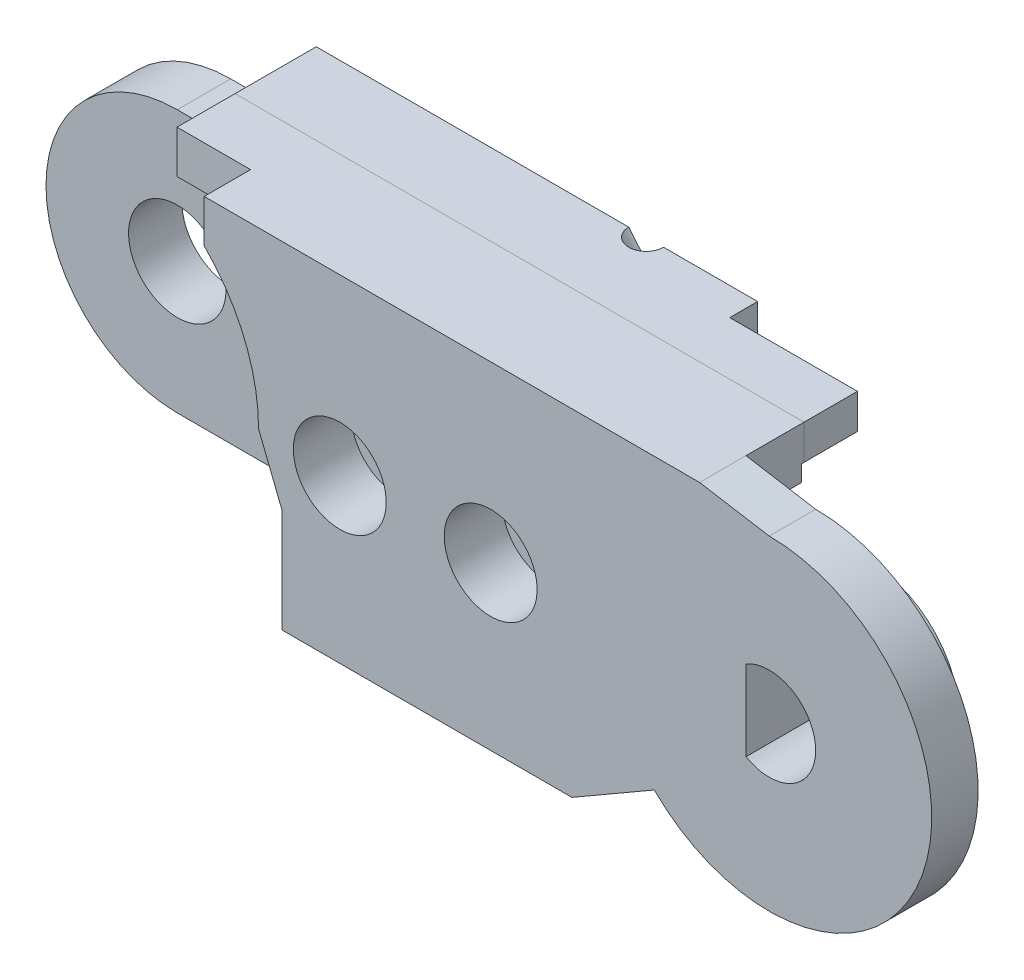
SolidWorks part; units mm, degrees
ref_plane "Front Plane" through (0, 0, 0) normal (0, 0, 1) x (1, 0, 0)
ref_plane "Top Plane" through (0, 0, 0) normal (0, 1, 0) x (1, 0, 0)
ref_plane "Right Plane" through (0, 0, 0) normal (1, 0, 0) x (0, 0, -1)
sketch "Sketch3" plane through (0, 0, 0) normal (0, 0, 1) x (1, 0, 0)
  line L7 (8, 0) -> (9, -2.5)
  line L11 (30, 7) -> (27, 7.5)
  line L13 (0, 7) -> (0, 7.5) construction
  line L14 (0, 7.5) -> (-22.3287, 7.5) construction
  line L15 (0, 5.3) -> (-14, 5.3) construction
  line L16 (0, 4) -> (-14, 4) construction
  line L17 (-14, 4) -> (-14, 5.3) construction
  line L18 (5.6569, 5.6569) -> (5.6569, 7.5)
  line L19 (5.6569, 7.5) -> (27, 7.5)
  line L20 (21.5, -7) -> (9, -7)
  line L21 (9, -7) -> (9, -2.5)
  line L23 (25.0503, -4.9497) -> (21.5, -7)
  arc A4 (8, 0) -> (5.6569, 5.6569) centre (0, 0) ccw
  arc A5 (25.0503, -4.9497) -> (30, 7) centre (30, 0) ccw
  circle A6 centre (0, 0) radius 7 construction
  circle A7 centre (0, 0) radius 3.9 construction
  circle A8 centre (0, 0) radius 5.3 construction
  circle A9 centre (0, 0) radius 4 construction
  dimension "D10" = 0.5
  dimension "D17" = 14
  dimension "D5" = 135
  dimension "D6" = 12.5
  dimension "D7" = 4.5
  dimension "D8" = 1
  dimension "D9" = 45
  dimension "D11" = 1.8431
  dimension "D12" = 30
  dimension "D14" = 3
extrude "Boss-Extrude1" add sketch "Sketch3" along normal blind 2 contours A5 L11 L19 L18 A4 L7 L21 L20 L23
sketch "Sketch20" plane through (0, 0, 0) normal (0, 0, 1) x (1, 0, 0)
  line L0 (0, 7) -> (0, 7.5) construction
  line L1 (0, 7.5) -> (-19.4737, 7.5) construction
  line L2 (0, 5.3) -> (-14, 5.3) construction
  line L3 (0, 4) -> (-14, 4) construction
  line L4 (-14, 4) -> (-14, 5.3) construction
  line L5 (0, 5.3) -> (17.4849, 5.3) construction
  line L6 (17.4849, 5.3) -> (17.4849, 4) construction
  line L7 (17.4849, 4) -> (0, 4) construction
  line L8 (-2.5, 7.5) -> (-2.5, 2.868) construction
  circle A0 centre (0, 0) radius 7 construction
  circle A1 centre (0, 0) radius 3.9 construction
  circle A3 centre (0, 0) radius 5.3 construction
  circle A4 centre (0, 0) radius 4 construction
  circle A5 centre (0, 0) radius 2 construction
  dimension "D1" = 0
  dimension "D2" = 2.5
ref_plane "Plane1" through (0, 0, 2) normal (0, 0, 1) x (1, 0, 0)
sketch "Sketch4" plane through (0, 0, 2) normal (0, 0, 1) x (1, 0, 0)
  line L4 (5.6569, 5.6569) -> (5.6569, 7.5)
  line L5 (5.6569, 5.6569) -> (5.6569, 7.5) construction
  line L6 (5.6569, 7.5) -> (21.5, 7.5)
  line L10 (8, 0) -> (9, -2.5)
  line L11 (9, -2.5) -> (9, -7)
  line L12 (9, -7) -> (21.5, -7)
  line L13 (21.5, -7) -> (21.5, 7.5)
  arc A0 (8, 0) -> (5.6569, 5.6569) centre (0, 0) ccw construction
  arc A3 (8, 0) -> (5.6569, 5.6569) centre (0, 0) ccw
sketch "Sketch22" plane through (0, 0, 2) normal (0, 0, 1) x (1, 0, 0)
  line L0 (5.6569, 5.6569) -> (2.4868, 5.6569)
  line L1 (5.6569, 7.5) -> (21.5, 7.5)
  line L2 (5.6569, 7.5) -> (2.4868, 7.5)
  line L3 (2.4868, 7.5) -> (2.4868, 5.6569)
  line L6 (8, 0) -> (9, -2.5)
  line L7 (9, -2.5) -> (9, -7)
  line L8 (9, -7) -> (21.5, -7)
  line L10 (21.5, 7.5) -> (27, 7.5)
  line L11 (27, 7.5) -> (27, 2.172)
  line L12 (27, 2.172) -> (23.2751, 2.172)
  line L13 (21.5, -7) -> (23.2751, -5.9749)
  line L14 (25.0503, -4.9497) -> (21.5, -7) construction
  line L15 (23.2751, -5.9749) -> (23.2751, 2.172)
  arc A0 (8, 0) -> (5.6569, 5.6569) centre (0, 0) ccw
extrude "Boss-Extrude6" add sketch "Sketch22" along normal blind 2.5
sketch "Sketch25" plane through (0, 0, 2) normal (0, 0, 1) x (1, 0, 0)
  line L0 (0, 5.3) -> (18.0981, 5.3) construction
  line L1 (0, 4) -> (18.0981, 4) construction
  line L2 (18.0981, 4) -> (18.0981, 5.3) construction
sketch "Sketch26" plane through (0, 0, 2) normal (0, 0, 1) x (1, 0, 0)
  line L1 (18.0981, 5.3) -> (2.5301, 5.3)
  line L2 (18.0981, 4) -> (2.5301, 4)
  line L3 (2.5301, 5.3) -> (2.5301, 4)
  line L4 (18.0981, 5.3) -> (27, 5.3)
  line L5 (27, 2.172) -> (27, 7.5) construction
  line L6 (27, 5.3) -> (27, 4)
  line L7 (27, 4) -> (18.0981, 4)
extrude "Cut-Extrude6" cut sketch "Sketch26" along normal blind 2.5
ref_plane "Plane18" through (0, 0, 4.5) normal (0, 0, 1) x (1, 0, 0)
sketch "Sketch31" plane through (0, 0, 4.5) normal (0, 0, 1) x (1, 0, 0)
  line L0 (2.4327, 5.6569) -> (0, 5.6569)
  line L4 (9, -5.6569) -> (0, -5.6569)
  line L5 (2.4327, 5.6569) -> (2.4868, 7.5)
  line L12 (9, -7) -> (9, -5.6569)
  line L13 (9, -2.5) -> (9, -7) construction
  line L16 (27, 7.5) -> (27, 2.172)
  line L17 (27, 2.172) -> (23.2751, 2.172)
  line L18 (23.2751, -5.9749) -> (23.2751, 2.172)
  line L19 (27, 7.5) -> (2.4868, 7.5)
  line L20 (9, -7) -> (21.5, -7)
  line L21 (21.5, -7) -> (23.2751, -5.9749)
  arc A0 (0, 5.6569) -> (0, -5.6569) centre (0, 0) ccw
  dimension "D1" = 5.6569
extrude "Boss-Extrude14" add sketch "Sketch31" along normal blind 2.3 separate body
sketch "Sketch32" plane through (0, 0, 6.8) normal (0, 0, 1) x (1, 0, 0)
  circle A0 centre (0, 0) radius 2.1
extrude "Cut-Extrude7" cut sketch "Sketch32" against normal blind 2.3
sketch "Sketch33" plane through (0, 0, 6.8) normal (0, 0, 1) x (1, 0, 0)
  line L4 (9, -5.6569) -> (9, -7)
  line L11 (9, -7) -> (21.5, -7)
  line L15 (21.5, -7) -> (21.5, -5.6569)
  line L16 (21.5, -5.6569) -> (9, -5.6569)
  line L17 (2.4868, 7.5) -> (21.5, 7.5)
  line L18 (27, 7.5) -> (2.4868, 7.5) construction
  line L19 (2.4868, 7.5) -> (2.4327, 5.6569)
  line L20 (2.4327, 5.6569) -> (21.5, 5.6569)
  line L21 (21.5, 5.6569) -> (21.5, 7.5)
extrude "Boss-Extrude15" add sketch "Sketch33" along normal blind 1.2
sketch "Sketch34" plane through (0, 0, 2) normal (0, 0, 1) x (1, 0, 0)
  line L0 (30, 5.3) -> (18.0981, 5.3) construction
  line L1 (30, 4) -> (18.0981, 4) construction
  circle A0 centre (30, 0) radius 2 construction
  circle A1 centre (30, 0) radius 5.3 construction
  circle A2 centre (30, 0) radius 4 construction
sketch "Sketch35" plane through (0, 0, 6.8) normal (0, 0, 1) x (1, 0, 0)
  line L0 (27, 2.172) -> (27, 6)
  line L1 (27, 2.172) -> (21.5204, 2.172)
  line L2 (27, 6) -> (21.5204, 6)
  line L3 (21.5204, 2.172) -> (21.5204, 6)
  line L4 (27, 2.172) -> (27, 7.5) construction
extrude "Cut-Extrude8" cut sketch "Sketch35" against normal blind 2.4
sketch "Sketch36" plane through (0, 0, 4.4) normal (0, 0, 1) x (1, 0, 0)
  line L0 (27, 2.172) -> (27, 4)
  line L1 (27, 2.172) -> (23.3, 2.172)
  line L2 (27, 4) -> (23.3, 4)
  line L3 (23.3, 2.172) -> (23.3, 4)
  line L4 (21.5, -7) -> (21.5, 7.5) construction
  dimension "D1" = 1.8
extrude "Cut-Extrude9" cut sketch "Sketch36" against normal blind 2.4
sketch "Sketch37" plane through (0, 0, 2) normal (0, 0, 1) x (1, 0, 0)
  circle A0 centre (30, 0) radius 3.9
extrude "Boss-Extrude16" add sketch "Sketch37" along normal blind 2.3
sketch "Sketch39" plane through (0, 0, 4.3) normal (0, 0, 1) x (1, 0, 0)
  line L0 (29, 1.7321) -> (29, -1.7321)
  arc A0 (29, -1.7321) -> (29, 1.7321) centre (30, 0) ccw
  dimension "D2" = 4
  dimension "D1" = 1
extrude "Cut-Extrude10" cut sketch "Sketch39" against normal through all
sketch "Sketch43" plane through (0, 0, 6.8) normal (0, 0, 1) x (1, 0, 0)
  line L2 (0, -5.6569) -> (9, -5.6569) construction
  circle A0 centre (11.5, 0) radius 2.5
  circle A1 centre (18, 0) radius 2.5
  dimension "D1" = 2.5
  dimension "D3" = 5
  dimension "D4" = 6.5
  dimension "D2" = 5.6569
extrude "Boss-Extrude17" add sketch "Sketch43" along normal blind 1.2
sketch "Sketch44" plane through (0, 0, 8) normal (0, 0, 1) x (1, 0, 0)
  circle A0 centre (11.5, 0) radius 0.95
  circle A1 centre (18, 0) radius 0.95
  dimension "D1" = 1.9
  dimension "D2" = 1.9
extrude "Cut-Extrude11" cut sketch "Sketch44" against normal through all
sketch "Sketch45" plane through (0, 0, 0) normal (0, 0, -1) x (-1, 0, 0)
  circle A0 centre (-11.5, 0) radius 2
  circle A1 centre (-18, 0) radius 2
extrude "Cut-Extrude12" cut sketch "Sketch45" against normal blind 2.5
ref_plane "Plane17" through (0, 0, 8) normal (0, 0, 1) x (1, 0, 0)
sketch "Sketch48" plane through (0, 0, 2) normal (0, 0, 1) x (1, 0, 0)
  circle A0 centre (30, 0) radius 5 construction
sketch "Sketch51" plane through (0, 0, 8) normal (0, 0, 1) x (1, 0, 0)
  line L0 (18.2355, 5.6569) -> (27.0112, -4.8677) construction
  line L1 (2.4327, 5.6569) -> (21.5, 5.6569) construction
sketch "Sketch52" plane through (0, 5.6569, 0) normal (0, -1, 0) x (1, 0, 0)
  circle A0 centre (18.2355, 8) radius 0.75
extrude "Cut-Extrude13" cut sketch "Sketch52" along direction (0.6404, -0.768, 0) on the side against the normal blind 10
mirror "Mirror1" about plane through (0, 0, 8) normal (0, 0, 1) of bodies 133 129
split "Split1" trim tools "Plane17" bodies to split 135 134 resulting bodies 136 137
delete or keep bodies "Body-Delete/Keep 1" type delete bodies bodies 129 133
